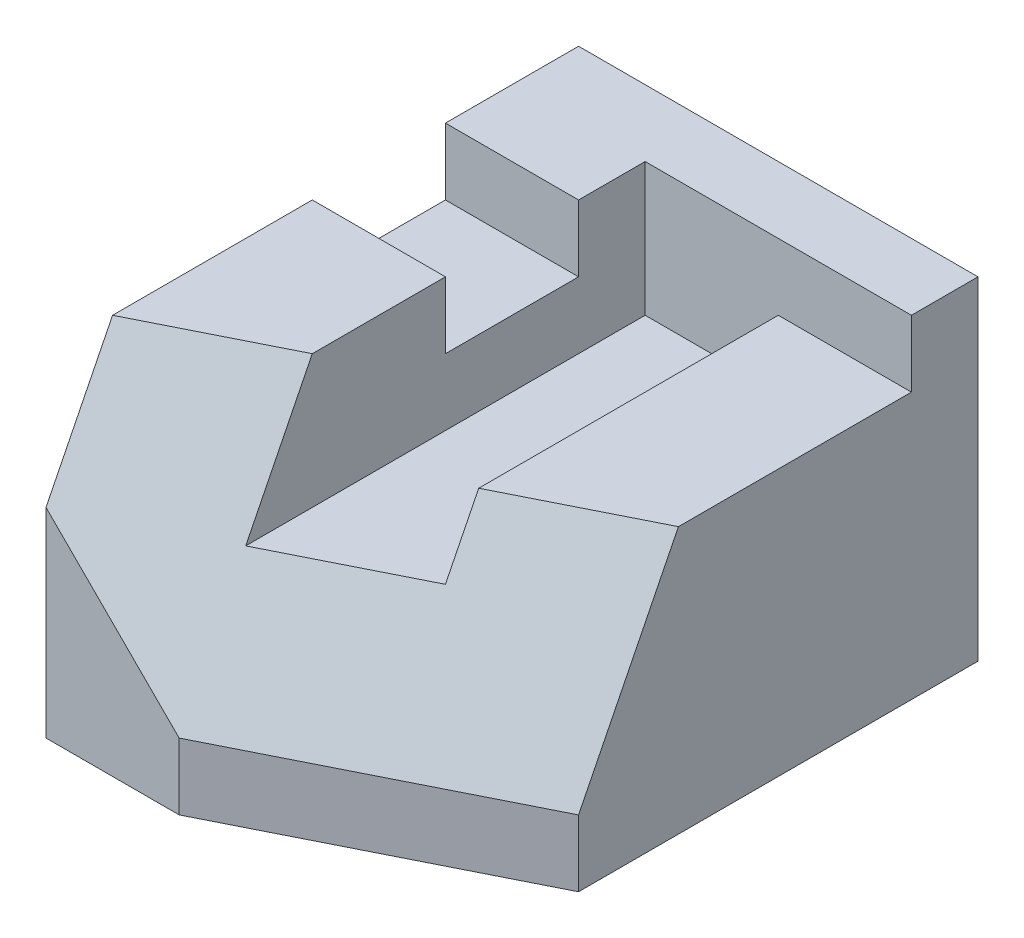
SolidWorks part; units mm, degrees
ref_plane "Front Plane" through (0, 0, 0) normal (0, 0, 1) x (1, 0, 0)
ref_plane "Top Plane" through (0, 0, 0) normal (0, 1, 0) x (1, 0, 0)
ref_plane "Right Plane" through (0, 0, 0) normal (1, 0, 0) x (0, 0, -1)
sketch "Sketch1" plane through (0, 0, 0) normal (0, 1, 0) x (1, 0, 0)
  line L1 (-30, -40) -> (30, -40)
  line L2 (-30, -40) -> (-30, 40)
  line L3 (-30, 40) -> (30, 40)
  line L4 (30, -40) -> (30, 40)
  line L5 (-30, -40) -> (30, 40) construction
  line L6 (-30, 40) -> (30, -40) construction
  point P0 (0, 0)
  dimension "D1" = 60
  dimension "D2" = 80
extrude "Boss-Extrude1" add sketch "Sketch1" along normal blind 50
sketch "Sketch2" plane through (0, 0, 40) normal (0, 0, 1) x (1, 0, 0)
  line L0 (30, 40) -> (10, 40)
  line L1 (30, 50) -> (30, 0) construction
  line L2 (10, 40) -> (10, 30)
  line L3 (10, 30) -> (-10, 30)
  line L4 (-10, 30) -> (-10, 50)
  line L5 (-30, 50) -> (30, 50) construction
  line L6 (-10, 50) -> (30, 50)
  line L7 (30, 50) -> (30, 40)
  dimension "D1" = 10
  dimension "D2" = 20
  dimension "D3" = 10
  dimension "D4" = 20
extrude "Cut-Extrude1" cut sketch "Sketch2" against normal blind 70
sketch "Sketch3" plane through (30, 0, 0) normal (1, 0, 0) x (0, 0, -1)
  line L0 (30, 40) -> (-40, 40) construction
  line L2 (-40, 0) -> (40, 0) construction
  line L3 (40, 50) -> (40, 0) construction
  point P0 (-5, 40)
  point P1 (-20, 10)
  dimension "D1" = 10
  dimension "D2" = 35
  dimension "D3" = 60
sketch "Sketch4" plane through (0, 0, 40) normal (0, 0, 1) x (1, 0, 0)
  line L0 (-30, 0) -> (30, 0) construction
  line L2 (-30, 50) -> (-30, 0) construction
  point P0 (-10, 10)
  point P6 (-30, 30)
  dimension "D1" = 10
  dimension "D2" = 20
  dimension "D3" = 30
sketch "Sketch5" plane through (0, 50, 0) normal (0, 1, 0) x (1, 0, 0)
  line L0 (-10, 30) -> (-10, -40) construction
  line L1 (-30, 40) -> (-30, -40) construction
  line L2 (30, 40) -> (-30, 40) construction
  point P0 (-10, -20)
  point P1 (-30, -30)
  dimension "D1" = 70
  dimension "D2" = 60
sketch "Sketch6" plane through (0, 30, 0) normal (0, 1, 0) x (1, 0, 0)
  line L0 (-10, 30) -> (-10, -40) construction
  point P0 (-10, -30)
  dimension "D1" = 60
sketch "Sketch7" plane through (-30, 0, 0) normal (-1, 0, 0) x (0, 0, 1)
  line L0 (-40, 50) -> (40, 50) construction
  line L1 (-20, 50) -> (0, 50)
  line L2 (-20, 50) -> (-20, 40)
  line L3 (-20, 40) -> (0, 40)
  line L4 (0, 50) -> (0, 40)
  line L5 (-40, 50) -> (-40, 0) construction
  dimension "D1" = 10
  dimension "D2" = 20
  dimension "D3" = 20
extrude "Cut-Extrude6" cut sketch "Sketch7" against normal blind 70
sketch "Sketch8" plane through (0, 0, 0) normal (0, -1, 0) x (1, 0, 0)
  line L0 (30, 40) -> (30, 20)
  line L1 (-30, 40) -> (30, 40) construction
  line L2 (30, 40) -> (30, -40) construction
  line L3 (30, 20) -> (-10, 40)
  line L4 (-10, 40) -> (30, 40)
  dimension "D1" = 40
  dimension "D2" = 20
extrude "Cut-Extrude7" cut sketch "Sketch8" against normal blind 70
sketch "Sketch9" plane through (0, 40, 0) normal (0, 1, 0) x (1, 0, 0)
  line L0 (10, 30) -> (10, -30) construction
  point P0 (10, -15)
  dimension "D1" = 45
sketch3d "3DSketch6"
  line L0 (-30, 50, 30) -> (-10, 50, 20)
  line L1 (-10, 50, 20) -> (-10, 30, 30)
  line L2 (-10, 30, 30) -> (10, 30, 20)
  line L3 (10, 30, -30) -> (10, 30, 30) construction
  line L4 (10, 30, 20) -> (10, 40, 15)
  line L5 (10, 40, 15) -> (30, 40, 5)
  line L6 (30, 40, 5) -> (30, 10, 20)
  line L7 (30, 10, 20) -> (-10, 10, 40)
  line L8 (-10, 10, 40) -> (-30, 30, 40)
  line L9 (-30, 30, 40) -> (-30, 50, 30)
  dimension "D1" = 50
extrude "Cut-Extrude8" cut sketch "3DSketch6" along direction (0, 0, -1) on the side of the normal blind 70
